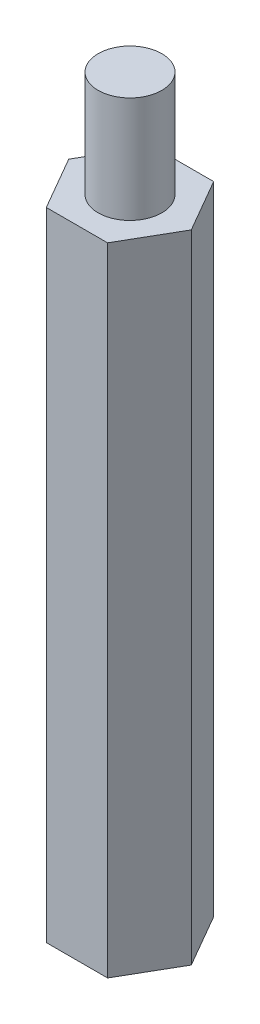
SolidWorks part; units mm, degrees
ref_plane "Front" through (0, 0, 0) normal (0, 0, 1) x (1, 0, 0)
ref_plane "Top" through (0, 0, 0) normal (0, 1, 0) x (1, 0, 0)
ref_plane "Right" through (0, 0, 0) normal (1, 0, 0) x (0, 0, -1)
sketch "草圖1" plane through (0, 0, 0) normal (0, 1, 0) x (1, 0, 0)
  line L1 (2.8868, 0) -> (1.4434, 2.5)
  line L2 (1.4434, 2.5) -> (-1.4434, 2.5)
  line L3 (-1.4434, 2.5) -> (-2.8868, 0)
  line L4 (-2.8868, 0) -> (-1.4434, -2.5)
  line L5 (-1.4434, -2.5) -> (1.4434, -2.5)
  line L6 (1.4434, -2.5) -> (2.8868, 0)
  circle A0 centre (0, 0) radius 2.5 construction
  dimension "D1" = 5
extrude "填料-伸長1" add sketch "草圖1" along normal blind 30
sketch "草圖2" plane through (0, 30, 0) normal (0, 1, 0) x (1, 0, 0)
  circle A0 centre (0, 0) radius 1.5
  dimension "D1" = 3
extrude "填料-伸長2" add sketch "草圖2" along normal blind 5
sketch "草圖3" plane through (0, 0, 0) normal (0, -1, 0) x (1, 0, 0)
  circle A0 centre (0, 0) radius 1.5
  dimension "D1" = 3
extrude "除料-伸長1" cut sketch "草圖3" against normal blind 5
